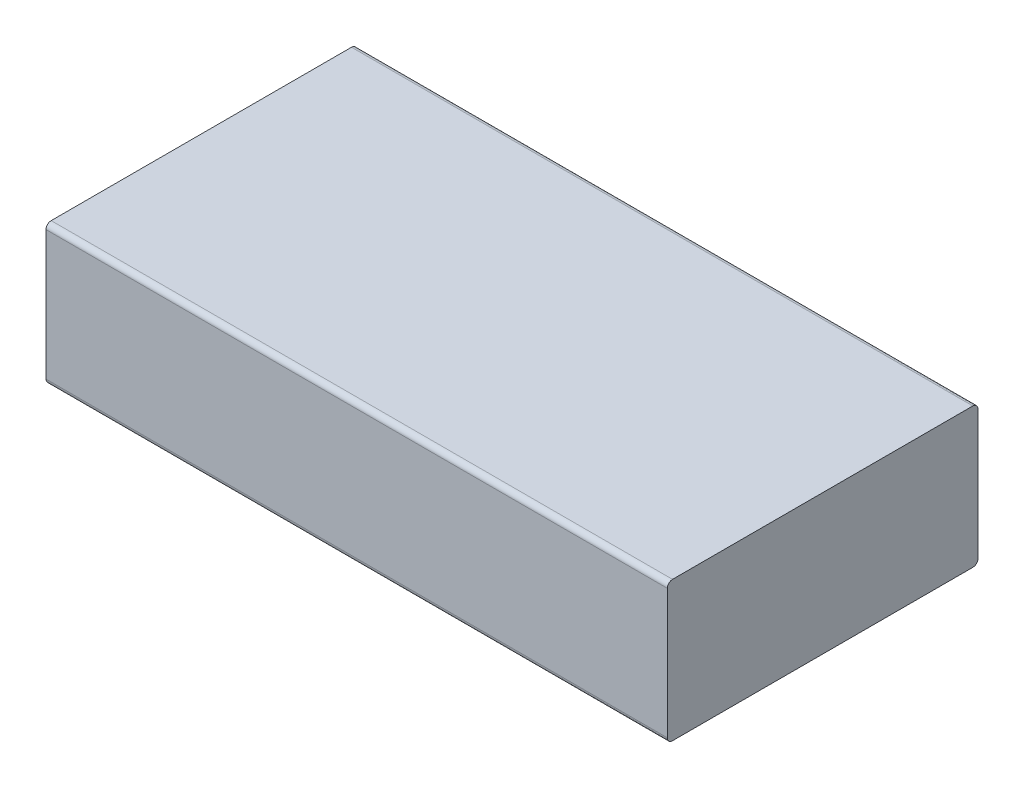
SolidWorks part; units mm, degrees
ref_plane "Front Plane" through (0, 0, 0) normal (0, 0, 1) x (1, 0, 0)
ref_plane "Top Plane" through (0, 0, 0) normal (0, 1, 0) x (1, 0, 0)
ref_plane "Right Plane" through (0, 0, 0) normal (1, 0, 0) x (0, 0, -1)
sketch "Sketch2" plane through (0, 0, 0) normal (1, 0, 0) x (0, 0, -1)
  line L1 (0, 0) -> (60, 0)
  line L2 (0, 0) -> (0, 27)
  line L3 (0, 27) -> (60, 27)
  line L4 (60, 0) -> (60, 27)
  dimension "D1" = 27
  dimension "D2" = 60
extrude "Boss-Extrude1" add sketch "Sketch2" along normal mid plane 120
fillet "Fillet1" radius 1 4 edges at (0, 0, -60) (0, 27, -60) (0, 0, 0) (0, 27, 0)
